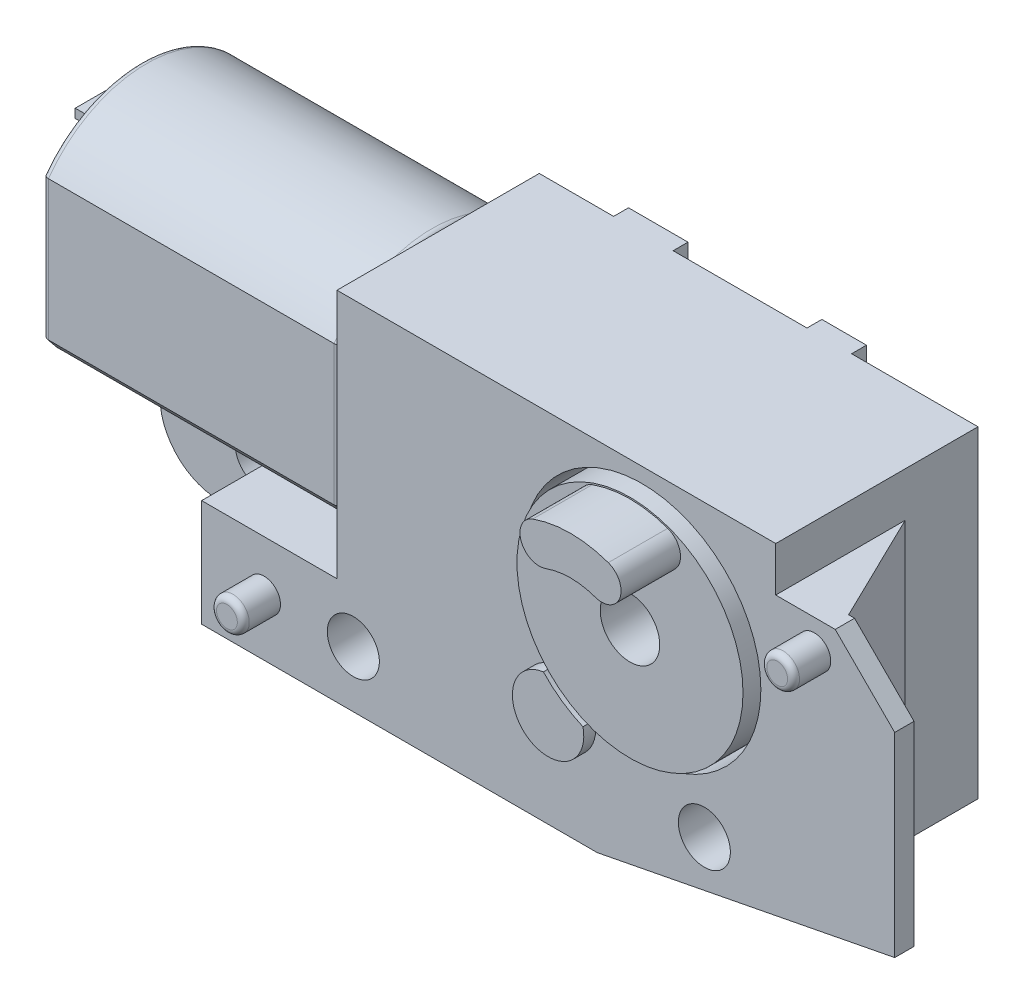
SolidWorks part; units mm, degrees
other "Body"
other "Motor"
other "Out-put_Gear"
ref_plane "Front" through (0, 0, 0) normal (0, 0, 1) x (1, 0, 0)
ref_plane "Top" through (0, 0, 0) normal (0, 1, 0) x (1, 0, 0)
ref_plane "Right" through (0, 0, 0) normal (1, 0, 0) x (0, 0, -1)
sketch "Sketch1" plane through (0, 0, 0) normal (0, 0, 1) x (1, 0, 0)
  line L0 (-10.25, 4.5) -> (4.5, 4.5)
  line L1 (-14.8, -7.5) -> (-1.5, -7.5)
  line L2 (-1.5, -7.5) -> (4.5, -6.3337)
  line L3 (-10.25, 4.5) -> (-10.25, -3.9)
  line L4 (4.5, -6.3337) -> (4.5, 4.5)
  line L5 (-10.25, -3.9) -> (-14.8, -3.9)
  line L6 (-14.8, -3.9) -> (-14.8, -7.5)
  dimension "D1" = 12
  dimension "D2" = 4.5
  dimension "D3" = 4.5
  dimension "D4" = 6
  dimension "D5" = 11
  dimension "D7" = 14.75
  dimension "D8" = 3.6
  dimension "D9" = 19.3
extrude "Boss-Extrude1" add sketch "Sketch1" along normal mid plane 6.8
sketch "Sketch2" plane through (-10.25, 0, 0) normal (-1, 0, 0) x (0, 0, 1)
  line L0 (0, 0) -> (0, 0.45) construction
  line L1 (3.4, 4.5) -> (-3.4, 4.5) construction
  line L2 (-3.3, 2.7979) -> (-3.3, -1.8979)
  line L3 (0, 0) -> (0, 3.1955) construction
  line L4 (3.3, 2.7979) -> (3.3, -1.8979)
  arc A0 (-3.3, -1.8979) -> (3.3, -1.8979) centre (0, 0.45) ccw
  arc A1 (3.3, 2.7979) -> (-3.3, 2.7979) centre (0, 0.45) ccw
  dimension "D1" = 8.1
  dimension "D2" = 6.6
extrude "Boss-Extrude2" add sketch "Sketch2" along normal blind 10 separate body
fillet "Fillet1" radius 0.2 8 edges at (-20.25, 0.45, 3.3) (-20.25, -3.6, 0) (-20.25, 0.45, -3.3) (-20.25, 4.5, 0) (-10.25, 0.45, 3.3) (-10.25, -3.6, 0) (-10.25, 0.45, -3.3) (-10.25, 4.5, 0)
sketch "Sketch3" plane through (0, 0, 3.4) normal (0, 0, 1) x (1, 0, 0)
  circle A0 centre (0, 0) radius 4
  dimension "D1" = 8
extrude "Cut-Extrude1" cut sketch "Sketch3" against normal blind 2
sketch "Sketch4" plane through (0, 0, 1.4) normal (0, 0, 1) x (1, 0, 0)
  circle A0 centre (0, 0) radius 3.8
  dimension "D1" = 7.6
extrude "Boss-Extrude3" add sketch "Sketch4" along normal blind 2.4 separate body
sketch "Sketch5" plane through (0, 0, 3.8) normal (0, 0, 1) x (1, 0, 0)
  circle A0 centre (0, 0) radius 1
  dimension "D1" = 2
extrude "Cut-Extrude2" cut sketch "Sketch5" against normal through all
sketch "Sketch6" plane through (0, 0, 3.8) normal (0, 0, 1) x (1, 0, 0)
  line L0 (0, 0) -> (0, 7.5834) construction
  line L1 (-1.7, 3.3425) -> (-1.7, 1.7642) construction
  line L2 (1.7, 3.3425) -> (1.7, 1.7642) construction
  arc A1 (0.8298, 2.3052) -> (-0.8298, 2.3052) centre (0, 0) ccw
  circle A2 centre (0, 0) radius 3.75
  arc A3 (1.2702, 3.5283) -> (-1.2702, 3.5283) centre (0, 0) ccw
  arc A4 (-1.2702, 3.5283) -> (-0.8298, 2.3052) centre (-1.05, 2.9168) ccw
  arc A5 (1.2702, 3.5283) -> (0.8298, 2.3052) centre (1.05, 2.9168) cw
  dimension "D2" = 1.3
  dimension "D3" = 3.4
  dimension "D1" = 0.05
extrude "Boss-Extrude4" add sketch "Sketch6" along normal blind 2
sketch "Sketch7" plane through (0, 0, 3.4) normal (0, 0, 1) x (1, 0, 0)
  line L0 (4.5, 3) -> (4.5, -6.3337)
  line L1 (4.5, -6.3337) -> (4.5, 4.5) construction
  line L2 (4.5, -6.3337) -> (8.5, -5.5562)
  line L3 (8.5, -5.5562) -> (8.5, 1)
  line L4 (8.5, 1) -> (6.5, 3)
  line L5 (6.5, 3) -> (4.5, 3)
  line L6 (-1.5, -7.5) -> (4.5, -6.3337) construction
  line L7 (4.5, 4.5) -> (-10.25, 4.5) construction
  dimension "D1" = 1.5
  dimension "D2" = 8.5
  dimension "D3" = 2
  dimension "D4" = 2
extrude "Boss-Extrude5" add sketch "Sketch7" against normal blind 0.65
sketch "Sketch8" plane through (0, 0, -3.4) normal (0, 0, -1) x (-1, 0, 0)
  line L0 (14.8, -7.5) -> (14.8, -3.9)
  line L1 (14.8, -3.9) -> (20.1, -3.9)
  line L2 (20.1, -3.9) -> (20.1, -5.5)
  line L3 (18.1, -7.5) -> (14.8, -7.5)
  line L4 (-4.5, 3) -> (-4.5, -6.3337) construction
  arc A0 (20.1, -5.5) -> (18.1, -7.5) centre (18.1, -5.5) cw
  dimension "D1" = 2
  dimension "D2" = 24.6
extrude "Boss-Extrude6" add sketch "Sketch8" against normal blind 2.9
sketch "Sketch9" plane through (0, 0, 0) normal (0, 0, 1) x (1, 0, 0)
  line L0 (-14.8, -7.5) -> (-1.5, -7.5) construction
  circle A0 centre (-16.7, -5.6) radius 0.875
  circle A1 centre (-9.7, -5.6) radius 0.875
  circle A2 centre (2.1, -5.25) radius 0.875
  dimension "D1" = 1.75
  dimension "D4" = 5.25
  dimension "D6" = 9.7
  dimension "D7" = 7
  dimension "D2" = 2.25
  dimension "D3" = 2.1
  dimension "D5" = 1.9
extrude "Cut-Extrude3" cut sketch "Sketch9" against normal through all and the other way through all
sketch "Sketch10" plane through (0, 0, 3.4) normal (0, 0, 1) x (1, 0, 0)
  line L0 (-9.7, -5.6) -> (-12.7, -5.6) construction
  line L1 (4.5, 4.5) -> (-10.25, 4.5) construction
  circle A0 centre (-12.7, -5.6) radius 0.55
  circle A1 centre (5.8, 2) radius 0.55
  dimension "D1" = 1.1
  dimension "D2" = 3
  dimension "D3" = 2.5
  dimension "D4" = 5.8
extrude "Boss-Extrude7" add sketch "Sketch10" along normal blind 1.25
fillet "Fillet2" radius 0.2 2 edges at (-12.15, -5.6, 4.65) (6.35, 2, 4.65)
sketch "Sketch11" plane through (0, 0, 3.4) normal (0, 0, 1) x (1, 0, 0)
  line L0 (0, 0) -> (0, -6.1813) construction
  line L1 (0, 0) -> (-2.7532, -3.9319) construction
  arc A0 (-2.9118, -2.7425) -> (-1.5812, -3.6742) centre (-2.7532, -3.9319) ccw
  circle A1 centre (0, 0) radius 3.8 construction
  circle A2 centre (0, 0) radius 4 construction
  arc A3 (-2.9118, -2.7425) -> (-1.5812, -3.6742) centre (0, 0) ccw
  dimension "D2" = 2.4
  dimension "D3" = 9.8
  dimension "D1" = 35
  dimension "D4" = 4.8
extrude "Boss-Extrude8" add sketch "Sketch11" along normal blind 0.4
sketch "Sketch12" plane through (-20.1, 0, 0) normal (-1, 0, 0) x (0, 0, 1)
  line L0 (3.4, -3.9) -> (-3.4, -3.9) construction
  line L1 (-0.5, -3.9) -> (-0.5, -7.5) construction
  line L2 (-1.0436, -4.4019) -> (-0.5, -4.3543)
  line L3 (-0.5, -5.5) -> (-0.5, -3.9) construction
  line L4 (-0.5, -4.3543) -> (-0.5, -5.4457)
  line L5 (-1, -4.9) -> (0, -4.9) construction
  line L6 (-1.0436, -5.3981) -> (-0.5, -5.4457)
  arc A0 (-1.0436, -4.4019) -> (-1.0436, -5.3981) centre (-1, -4.9) ccw
  dimension "D1" = 1
  dimension "D2" = 1
  dimension "D3" = 85
extrude "Boss-Extrude9" add sketch "Sketch12" along normal blind 1
sketch "Sketch13" plane through (-20.25, 0, 0) normal (-1, 0, 0) x (0, 0, 1)
  circle A0 centre (0, 0.45) radius 1.75
  dimension "D1" = 3.5
extrude "Boss-Extrude10" add sketch "Sketch13" along normal blind 1
fillet "Fillet3" radius 0.2 1 edges at (-21.25, -1.3, 0)
sketch "Sketch14" plane through (-20.25, 0, 0) normal (-1, 0, 0) x (0, 0, 1)
  line L0 (0, 0.45) -> (0, 3.2) construction
  line L1 (0, 0.45) -> (0, -2.3) construction
  line L2 (0, 3.2) -> (1.2, 3.2)
  line L3 (0, 3.2) -> (0, 2.9)
  line L4 (0, 2.9) -> (1.2, 2.9)
  line L5 (1.2, 3.2) -> (1.2, 2.9)
  line L7 (0, -2.3) -> (-1.2, -2.3)
  line L8 (0, -2.3) -> (0, -2)
  line L9 (0, -2) -> (-1.2, -2)
  line L10 (-1.2, -2.3) -> (-1.2, -2)
  arc A0 (3.3, 2.7979) -> (-3.3, 2.7979) centre (0, 0.45) ccw construction
  dimension "D1" = 5.5
  dimension "D2" = 0.3
  dimension "D3" = 1.2
extrude "Boss-Extrude11" add sketch "Sketch14" along normal blind 1
sketch "Sketch15" plane through (0, 0, 0) normal (0, 1, 0) x (1, 0, 0)
  line L0 (4.5, -2.75) -> (6.3, -2.75)
  line L2 (6.3, -2.75) -> (4.5, 0.95)
  line L3 (4.5, -3.4) -> (4.5, 3.4) construction
  line L4 (4.5, 0.95) -> (4.5, -2.75)
  line L5 (8.5, -2.75) -> (6.5, -2.75) construction
  line L6 (8.5, -2.75) -> (8.5, -3.4) construction
  dimension "D1" = 2.2
  dimension "D2" = 3.7
extrude "Boss-Extrude12" add sketch "Sketch15" along normal up to surface and the other way up to surface up to face at (5.75, 3, 2.9937) other way up to face at (3.5, -6.5281, 1.4292)
sketch "Sketch16" plane through (0, 0, -3.4) normal (0, 0, -1) x (-1, 0, 0)
  line L0 (-4.5, 4.5) -> (10.25, 4.5) construction
  line L1 (7.75, 4.5) -> (-0.25, 4.5)
  line L2 (7.75, 4.5) -> (7.75, -7.5)
  line L3 (7.75, -7.5) -> (1.5, -7.5)
  line L4 (-0.25, 4.5) -> (-0.25, -7.1598)
  line L5 (18.1, -7.5) -> (1.5, -7.5) construction
  line L6 (20.25, 2.7331) -> (20.25, -1.8331) construction
  line L7 (1.5, -7.5) -> (-4.5, -6.3337) construction
  line L8 (1.5, -7.5) -> (-0.25, -7.1598)
  dimension "D1" = 12.5
  dimension "D2" = 20.5
extrude "Boss-Extrude13" add sketch "Sketch16" along normal blind 0.5
sketch "Sketch17" plane through (0, 4.5, 0) normal (0, 1, 0) x (1, 0, 0)
  line L0 (-7.75, 3.9) -> (0.25, 3.9) construction
  line L1 (-5.75, 3.9) -> (-1.25, 3.9)
  line L2 (-5.75, 3.9) -> (-5.75, 3.4)
  line L3 (-5.75, 3.4) -> (-1.25, 3.4)
  line L4 (-1.25, 3.9) -> (-1.25, 3.4)
  line L5 (-4.65, 3.4) -> (-1.65, 3.4) construction
  line L6 (-20.25, 3.1) -> (-20.25, -3.1) construction
  dimension "D1" = 14.5
  dimension "D2" = 19
extrude "Cut-Extrude4" cut sketch "Sketch17" against normal through all
